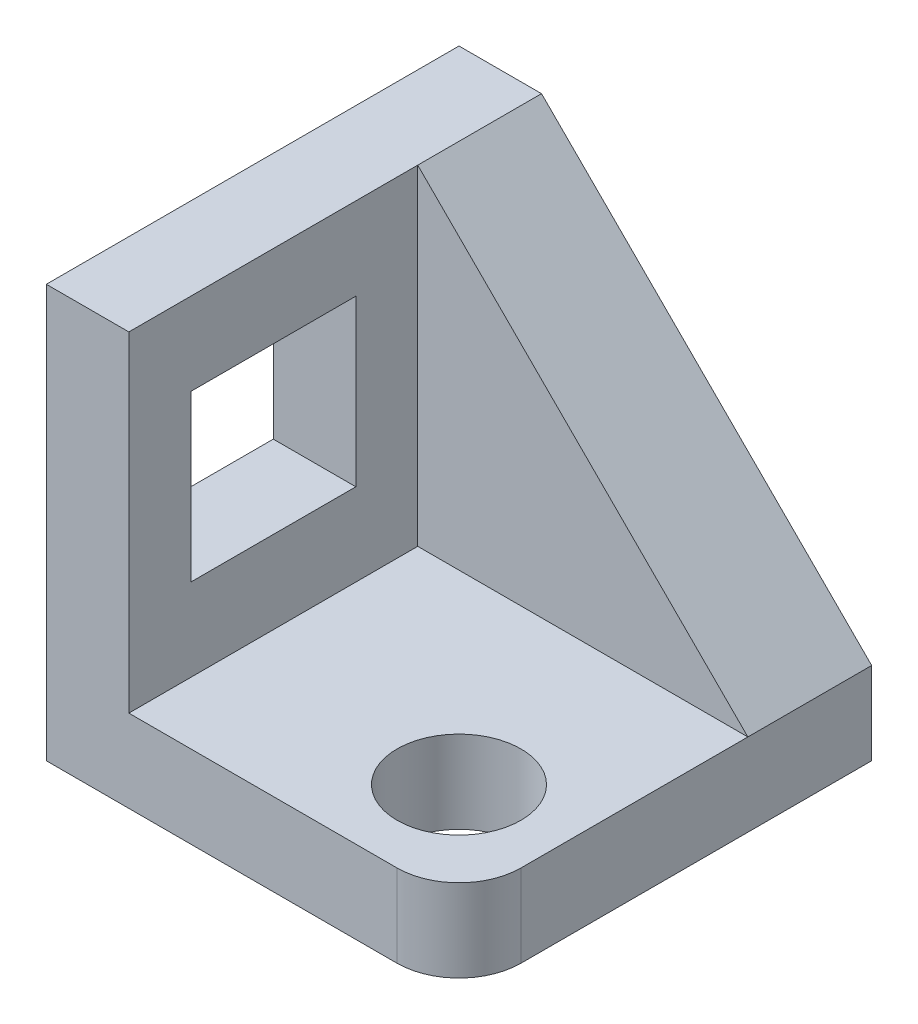
SolidWorks part; units mm, degrees
material "Resina de poliéster"
ref_plane "Alzado" through (0, 0, 0) normal (0, 0, 1) x (1, 0, 0)
ref_plane "Planta" through (0, 0, 0) normal (0, 1, 0) x (1, 0, 0)
ref_plane "Vista lateral" through (0, 0, 0) normal (1, 0, 0) x (0, 0, -1)
sketch "Croquis1" plane through (0, 0, 0) normal (0, 1, 0) x (1, 0, 0)
  line L1 (-50, 50) -> (50, 50)
  line L2 (-50, 50) -> (-50, -50)
  line L3 (-50, -50) -> (50, -50)
  line L4 (50, 50) -> (50, -50)
  line L5 (-50, 50) -> (50, -50) construction
  line L6 (-50, -50) -> (50, 50) construction
  point P0 (0, 0)
  dimension "D1" = 100
  dimension "D2" = 100
extrude "Saliente-Extruir1" add sketch "Croquis1" along normal blind 20
sketch "Croquis2" plane through (0, 20, 0) normal (0, 1, 0) x (1, 0, 0)
  line L0 (-50, -50) -> (50, -50) construction
  line L1 (-50, 50) -> (-30, 50)
  line L2 (-50, 50) -> (-50, -50)
  line L3 (-50, -50) -> (-30, -50)
  line L4 (-30, 50) -> (-30, -50)
  dimension "D1" = 20
extrude "Saliente-Extruir2" add sketch "Croquis2" along normal blind 80
sketch "Croquis3" plane through (0, 20, 0) normal (0, 1, 0) x (1, 0, 0)
  line L0 (50, -50) -> (50, 50) construction
  line L1 (-30, 50) -> (50, 50)
  line L2 (-30, 50) -> (-30, 20)
  line L3 (-30, 20) -> (50, 20)
  line L4 (50, 50) -> (50, 20)
  dimension "D1" = 30
extrude "Saliente-Extruir3" add sketch "Croquis3" along normal blind 80
sketch "Croquis4" plane through (0, 0, -20) normal (0, 0, 1) x (1, 0, 0)
  line L0 (50, 20) -> (-30, 100)
  line L1 (-30, 100) -> (50, 100)
  line L2 (50, 100) -> (50, 20)
extrude "Cortar-Extruir1" cut sketch "Croquis4" against normal blind 80
sketch "Croquis5" plane through (0, 20, 0) normal (0, 1, 0) x (1, 0, 0)
  line L0 (-30, -50) -> (50, -50) construction
  line L1 (50, -50) -> (50, 20) construction
  circle A0 centre (25, -25) radius 15
  dimension "D1" = 25
  dimension "D2" = 25
extrude "Cortar-Extruir2" cut sketch "Croquis5" against normal blind 80
fillet "Redondeo1" radius 15 1 edges at (50, 10, 50)
sketch "Croquis6" plane through (-30, 0, 0) normal (1, 0, 0) x (0, 0, -1)
  line L0 (20, 100) -> (20, 20) construction
  line L1 (5, 80) -> (-35, 80)
  line L2 (5, 80) -> (5, 40)
  line L3 (5, 40) -> (-35, 40)
  line L4 (-35, 80) -> (-35, 40)
  line L5 (-50, 100) -> (20, 100) construction
  dimension "D1" = 40
  dimension "D2" = 40
  dimension "D3" = 15
  dimension "D4" = 20
extrude "Cortar-Extruir3" cut sketch "Croquis6" against normal blind 80
